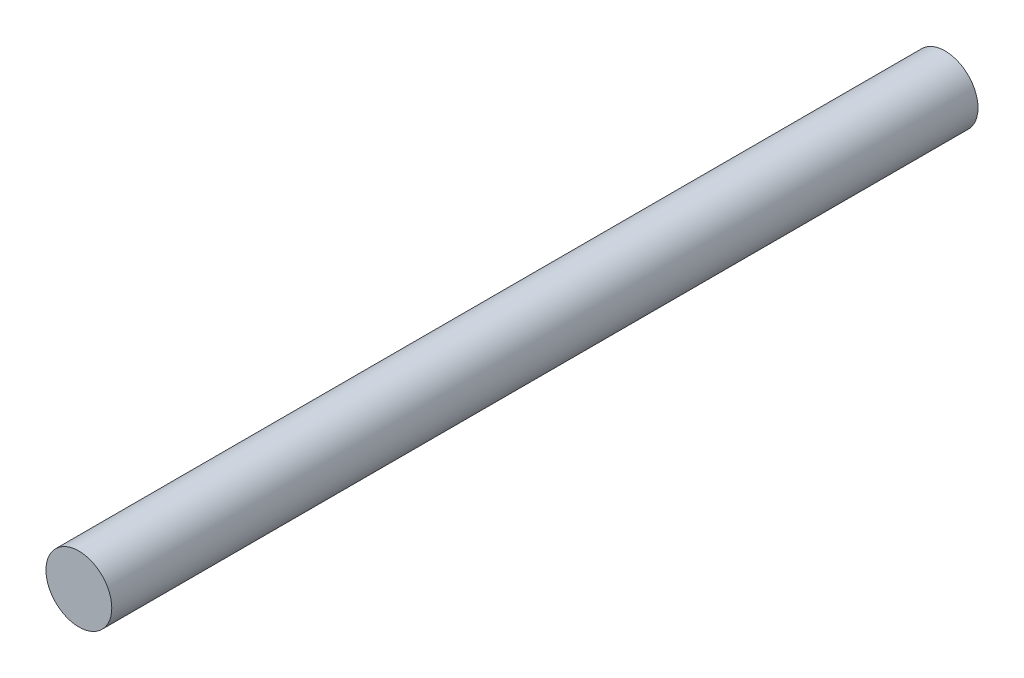
SolidWorks part; units mm, degrees
ref_plane "前视基准面" through (0, 0, 0) normal (0, 0, 1) x (1, 0, 0)
ref_plane "上视基准面" through (0, 0, 0) normal (0, 1, 0) x (1, 0, 0)
ref_plane "右视基准面" through (0, 0, 0) normal (1, 0, 0) x (0, 0, -1)
sketch "草图1" plane through (0, 0, 0) normal (0, 0, 1) x (1, 0, 0)
  circle A0 centre (2.7888, 15.199) radius 4
extrude "凸台-拉伸1" add sketch "草图1" along normal blind 105.25
ref_plane "基准面1" through (0, 0, 55.25) normal (0, 0, 1) x (1, 0, 0)
